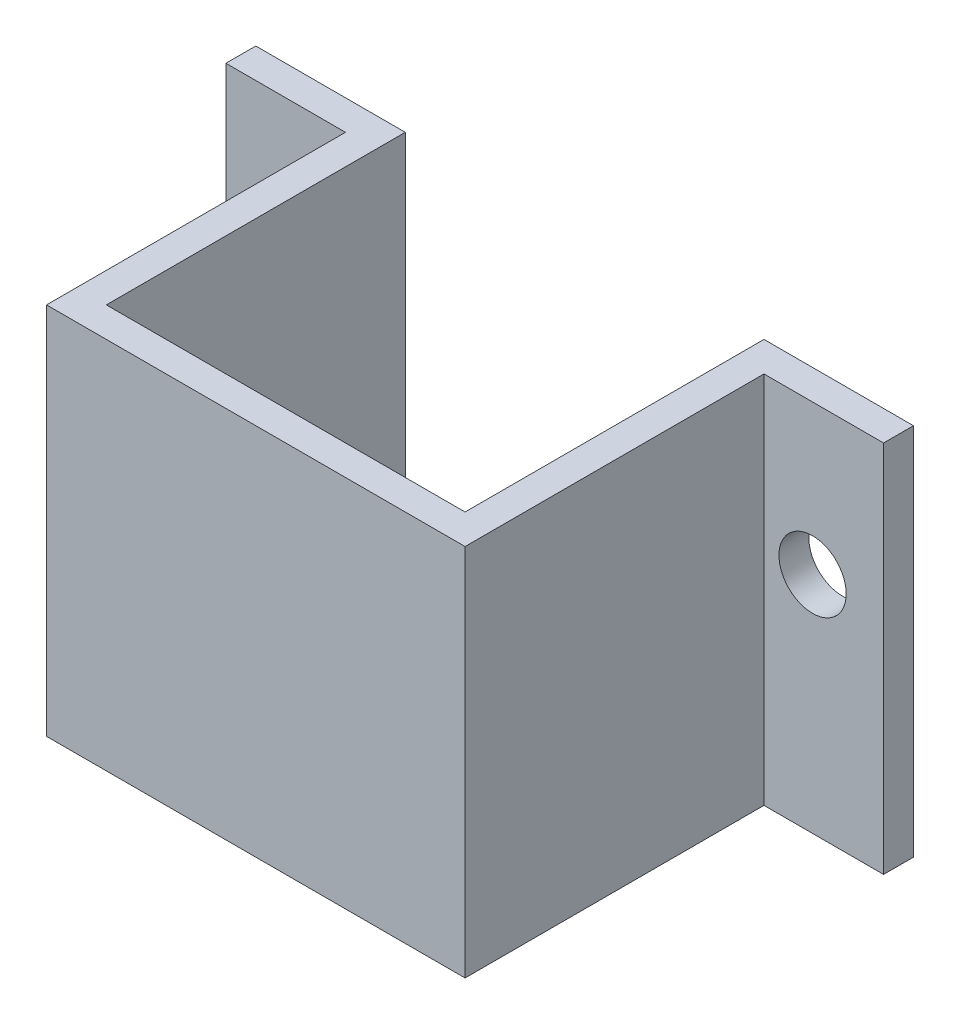
SolidWorks part; units mm, degrees
ref_plane "Front Plane" through (0, 0, 0) normal (0, 0, 1) x (1, 0, 0)
ref_plane "Top Plane" through (0, 0, 0) normal (0, 1, 0) x (1, 0, 0)
ref_plane "Right Plane" through (0, 0, 0) normal (1, 0, 0) x (0, 0, -1)
sketch "Sketch2" plane through (0, 0, 0) normal (0, 0, 1) x (1, 0, 0)
  line L1 (-10.0285, 7.1309) -> (3.9715, 7.1309)
  line L2 (-10.0285, 7.1309) -> (-10.0285, -5.3691)
  line L3 (-10.0285, -5.3691) -> (3.9715, -5.3691)
  line L4 (3.9715, 7.1309) -> (3.9715, -5.3691)
  dimension "D1" = 12.5
  dimension "D2" = 14
  dimension "D3" = 1.625
extrude "Boss-Extrude1" add sketch "Sketch2" along normal blind 11
sketch "Sketch3" plane through (0, -5.3691, 0) normal (0, -1, 0) x (-1, 0, 0)
  line L0 (10.0285, 0) -> (-3.9715, 0) construction
  line L1 (9.0285, 0) -> (-2.9715, 0)
  line L2 (9.0285, 0) -> (9.0285, -10)
  line L3 (9.0285, -10) -> (-2.9715, -10)
  line L4 (-2.9715, 0) -> (-2.9715, -10)
  line L5 (-3.9715, -11) -> (-3.9715, 0) construction
  dimension "D1" = 12
  dimension "D2" = 10
  dimension "D3" = 1
extrude "Cut-Extrude1" cut sketch "Sketch3" against normal blind 12.5
sketch "Sketch4" plane through (3.9715, 0, 0) normal (1, 0, 0) x (0, 0, -1)
  line L0 (-11, -5.3691) -> (0, -5.3691) construction
  line L1 (0, 7.1309) -> (-1, 7.1309)
  line L2 (0, 7.1309) -> (0, -5.3691)
  line L3 (0, -5.3691) -> (-1, -5.3691)
  line L4 (-1, 7.1309) -> (-1, -5.3691)
  dimension "D1" = 1
extrude "Boss-Extrude2" add sketch "Sketch4" along normal blind 4
sketch "Sketch5" plane through (-10.0285, 0, 0) normal (-1, 0, 0) x (0, 0, 1)
  line L0 (11, -5.3691) -> (0, -5.3691) construction
  line L1 (0, 7.1309) -> (1, 7.1309)
  line L2 (0, 7.1309) -> (0, -5.3691)
  line L3 (0, -5.3691) -> (1, -5.3691)
  line L4 (1, 7.1309) -> (1, -5.3691)
  dimension "D1" = 1
extrude "Boss-Extrude3" add sketch "Sketch5" along normal blind 4
sketch "Sketch6" plane through (0, 0, 1) normal (0, 0, 1) x (1, 0, 0)
  line L0 (-14.0285, -5.3691) -> (-10.0285, -5.3691) construction
  line L1 (7.9715, -5.3691) -> (3.9715, -5.3691) construction
  line L2 (3.9715, 7.1309) -> (3.9715, -5.3691) construction
  line L3 (-10.0285, 7.1309) -> (-10.0285, -5.3691) construction
  circle A0 centre (-11.6535, 2.1309) radius 1.125
  circle A1 centre (5.5965, 2.1309) radius 1.125
  dimension "D1" = 2.25
  dimension "D2" = 2.25
  dimension "D3" = 7.5
  dimension "D4" = 7.5
  dimension "D5" = 1.625
  dimension "D6" = 1.625
extrude "Cut-Extrude2" cut sketch "Sketch6" against normal blind 1
